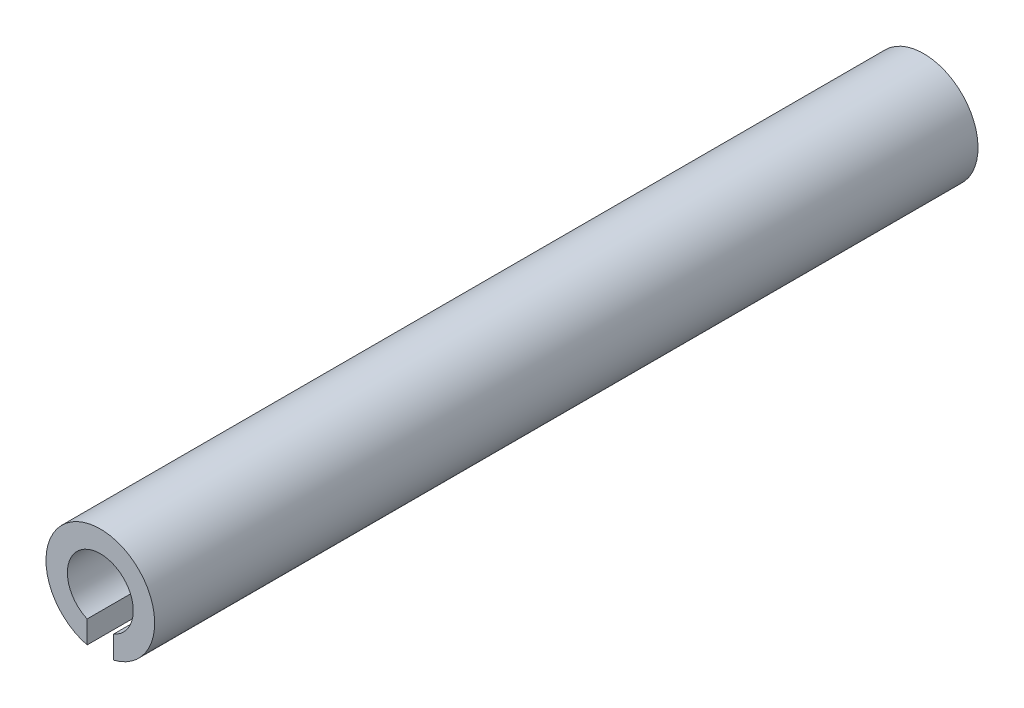
SolidWorks part; units mm, degrees
ref_plane "Front Plane" through (0, 0, 0) normal (0, 0, 1) x (1, 0, 0)
ref_plane "Top Plane" through (0, 0, 0) normal (0, 1, 0) x (1, 0, 0)
ref_plane "Right Plane" through (0, 0, 0) normal (1, 0, 0) x (0, 0, -1)
sketch "Sketch1" plane through (0, 0, 0) normal (0, 0, 1) x (1, 0, 0)
  line L1 (-0.4, 0) -> (0.4, 0)
  line L2 (-0.4, 0) -> (-0.4, -2.2024)
  line L3 (-0.4, -2.2024) -> (0.4, -2.2024)
  line L4 (0.4, 0) -> (0.4, -2.2024)
  circle A0 centre (0, 0) radius 1.65
  circle A1 centre (0, 0) radius 1
  dimension "D1" = 3.3
  dimension "D2" = 2
  dimension "D4" = 0.4
  dimension "D3" = 0.8
  dimension "D5" = 2.2024
  dimension "D6" = 0.4
extrude "dowel_body" add sketch "Sketch1" along normal blind 25 contours A1 L4 A0 L2
